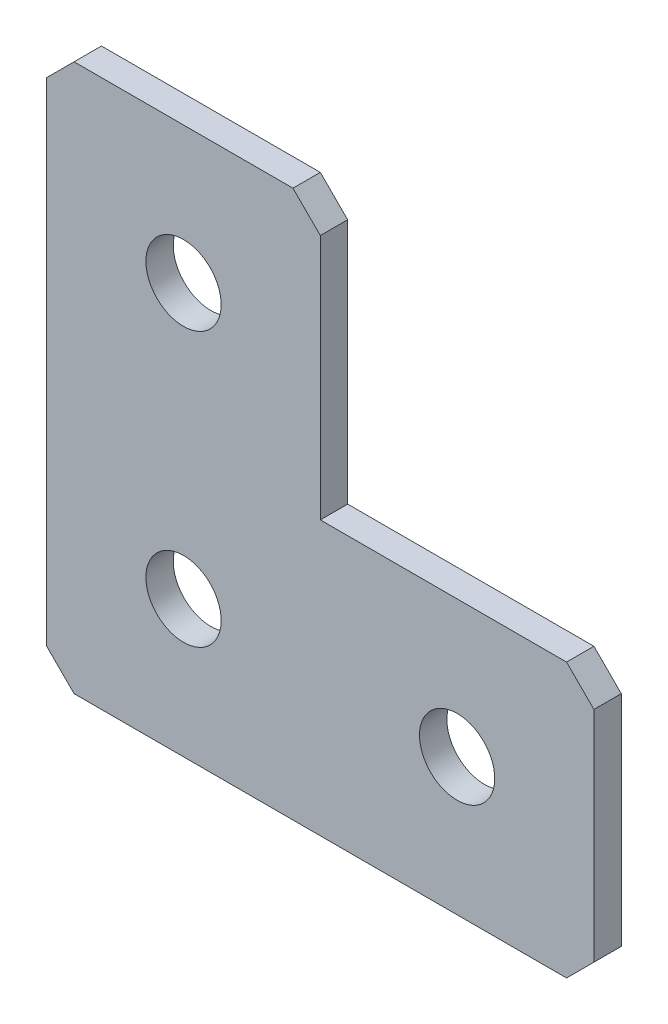
SolidWorks part; units mm, degrees
material "Простая углеродистая сталь"
ref_plane "Спереди(Плоскость XY)" through (0, 0, 0) normal (0, 0, 1) x (1, 0, 0)
ref_plane "Сверху(Плоскость XZ)" through (0, 0, 0) normal (0, 1, 0) x (1, 0, 0)
ref_plane "Справа(Плоскость ZY)" through (0, 0, 0) normal (1, 0, 0) x (0, 0, -1)
sketch "Эскиз1" plane through (0, 0, 0) normal (0, 0, -1) x (1, 0, 0)
  line L0 (0, 0) -> (0, 40)
  line L1 (0, 40) -> (40, 40)
  line L2 (40, 40) -> (40, 20)
  line L3 (40, 20) -> (20, 20)
  line L4 (20, 20) -> (20, 0)
  line L5 (20, 0) -> (0, 0)
  dimension "D1" = 40
  dimension "D2" = 20
  dimension "D3" = 20
  dimension "D4" = 20
extrude "Бобышка-Вытянуть1" add sketch "Эскиз1" along normal blind 2
hole_wizard "Отверстие с зазором M51" positions "Эскиз2" profile "Эскиз3" hole size "M5" standard "DIN" end condition through all
sketch "Эскиз2" plane through (0, 0, -2) normal (0, 0, -1) x (1, 0, 0)
  line L0 (10, 0) -> (10, 40) construction
  line L1 (0, 0) -> (20, 0) construction
  line L2 (40, 40) -> (0, 40) construction
  line L3 (40, 30) -> (0, 30) construction
  line L4 (40, 20) -> (40, 40) construction
  line L5 (0, 40) -> (0, 0) construction
  point P0 (10, 30)
  point P4 (10, 30)
  point P6 (10, 10)
  point P21 (30, 30)
  dimension "D1" = 20
  dimension "D2" = 20
  dimension "D4" = 10
sketch "Эскиз3" plane through (10, -30, -2) normal (1, 0, 0) x (0, 1, 0)
  line L0 (0, 0) -> (0, 2)
  line L1 (0, 2) -> (2.75, 2)
  line L2 (2.75, 2) -> (2.75, 0)
  line L5 (2.75, 0) -> (0, 0)
  line L11 (0, -6.35) -> (0, 107.95) construction
  dimension "Диаметр сквозного отверстия" = 5.5
  dimension "Глубина сквозного отверстия" = 2
chamfer "Фаска1" distance 2 angle 45 5 edges at (0, 0, -1) (20, 0, -1) (40, -20, -1) (40, -40, -1) (0, -40, -1)
